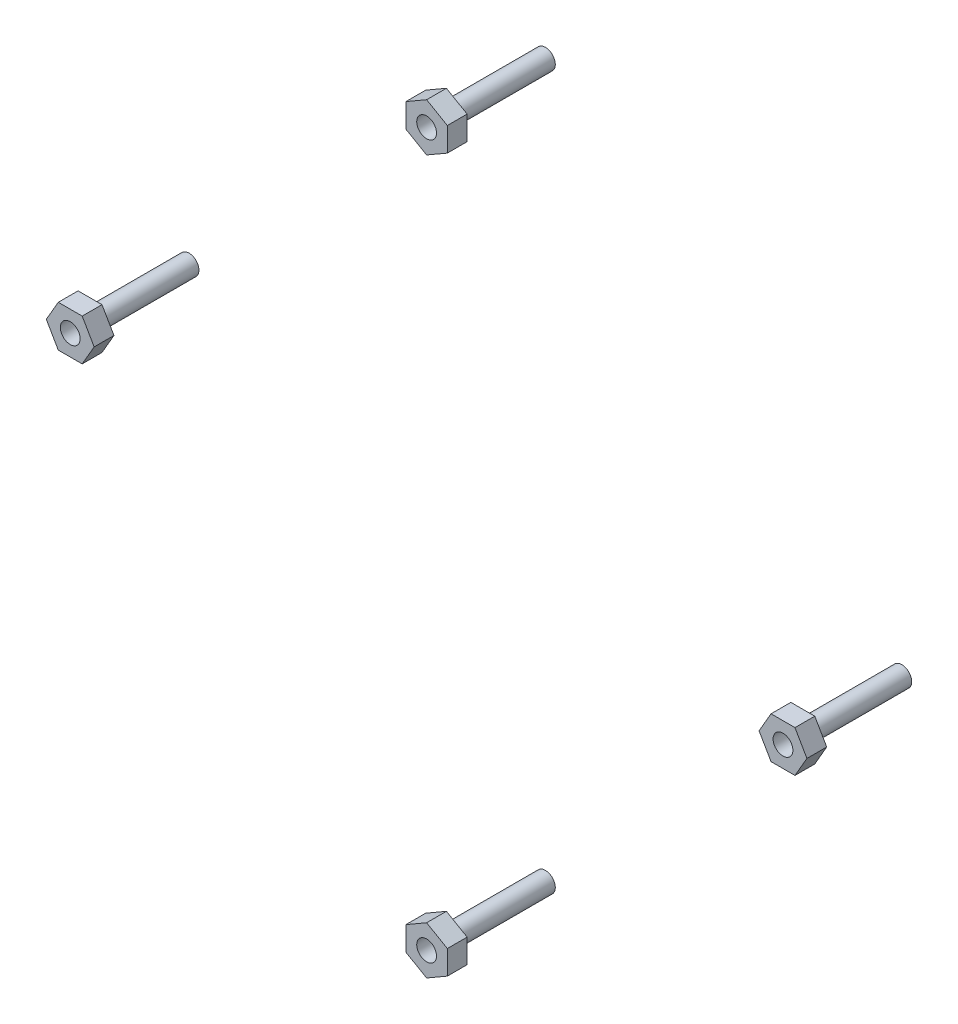
SolidWorks part; units mm, degrees
ref_plane "Front Plane" through (0, 0, 0) normal (0, 0, 1) x (1, 0, 0)
ref_plane "Top Plane" through (0, 0, 0) normal (0, 1, 0) x (1, 0, 0)
ref_plane "Right Plane" through (0, 0, 0) normal (1, 0, 0) x (0, 0, -1)
sketch "Sketch1" plane through (0, 0, 0) normal (0, 0, 1) x (1, 0, 0)
  circle A0 centre (0, 0) radius 54
  dimension "D1" = 108
sketch "Sketch2" plane through (0, 0, 0) normal (0, 0, 1) x (1, 0, 0)
  circle A0 centre (0, 54) radius 1.5
  circle A1 centre (0, 0) radius 54 construction
  circle A2 centre (54, 0) radius 1.5
  circle A3 centre (0, -54) radius 1.5
  circle A4 centre (-54, 0) radius 1.5
  point P4 (0, 0)
  dimension "D1" = 3
  dimension "D2" = 4
extrude "Boss-Extrude1" add sketch "Sketch2" along normal blind 15
ref_plane "Plane1" through (0, 0, 15) normal (0, 0, 1) x (1, 0, 0)
sketch "Sketch3" plane through (0, 0, 15) normal (0, 0, 1) x (1, 0, 0)
  line L0 (55.8126, -3.1395) -> (57.6251, 0)
  line L1 (3.1395, 55.8126) -> (0, 57.6251)
  line L2 (0, 57.6251) -> (-3.1395, 55.8126)
  line L3 (-3.1395, 55.8126) -> (-3.1395, 52.1874)
  line L4 (-3.1395, 52.1874) -> (0, 50.3749)
  line L5 (0, 50.3749) -> (3.1395, 52.1874)
  line L6 (3.1395, 52.1874) -> (3.1395, 55.8126)
  line L7 (57.6251, 0) -> (55.8126, 3.1395)
  line L8 (55.8126, 3.1395) -> (52.1874, 3.1395)
  line L9 (52.1874, 3.1395) -> (50.3749, 0)
  line L10 (50.3749, 0) -> (52.1874, -3.1395)
  line L11 (52.1874, -3.1395) -> (55.8126, -3.1395)
  line L12 (-3.1395, -55.8126) -> (0, -57.6251)
  line L13 (0, -57.6251) -> (3.1395, -55.8126)
  line L14 (3.1395, -55.8126) -> (3.1395, -52.1874)
  line L15 (3.1395, -52.1874) -> (0, -50.3749)
  line L16 (0, -50.3749) -> (-3.1395, -52.1874)
  line L17 (-3.1395, -52.1874) -> (-3.1395, -55.8126)
  line L18 (-55.8126, 3.1395) -> (-57.6251, 0)
  line L19 (-57.6251, 0) -> (-55.8126, -3.1395)
  line L20 (-55.8126, -3.1395) -> (-52.1874, -3.1395)
  line L21 (-52.1874, -3.1395) -> (-50.3749, 0)
  line L22 (-50.3749, 0) -> (-52.1874, 3.1395)
  line L23 (-52.1874, 3.1395) -> (-55.8126, 3.1395)
  circle A0 centre (0, 54) radius 3.1395 construction
  circle A4 centre (-54, 0) radius 1.5
  circle A5 centre (-54, 0) radius 1.5
  circle A6 centre (0, -54) radius 1.5
  circle A7 centre (0, -54) radius 1.5
  circle A8 centre (54, 0) radius 1.5
  circle A9 centre (54, 0) radius 1.5
  circle A10 centre (0, 54) radius 1.5
  circle A11 centre (0, 54) radius 1.5
  point P1 (0, 0)
  point P10 (0, 0)
  point P12 (0, 0)
  point P31 (0, 0)
  point P32 (0, 0)
  dimension "D2" = 4
  dimension "D1" = 3.6251
  dimension "D4" = 0
  dimension "D5" = 0
  dimension "D6" = 0
  dimension "D7" = 0
extrude "Boss-Extrude2" add sketch "Sketch3" along normal blind 3 separate body
